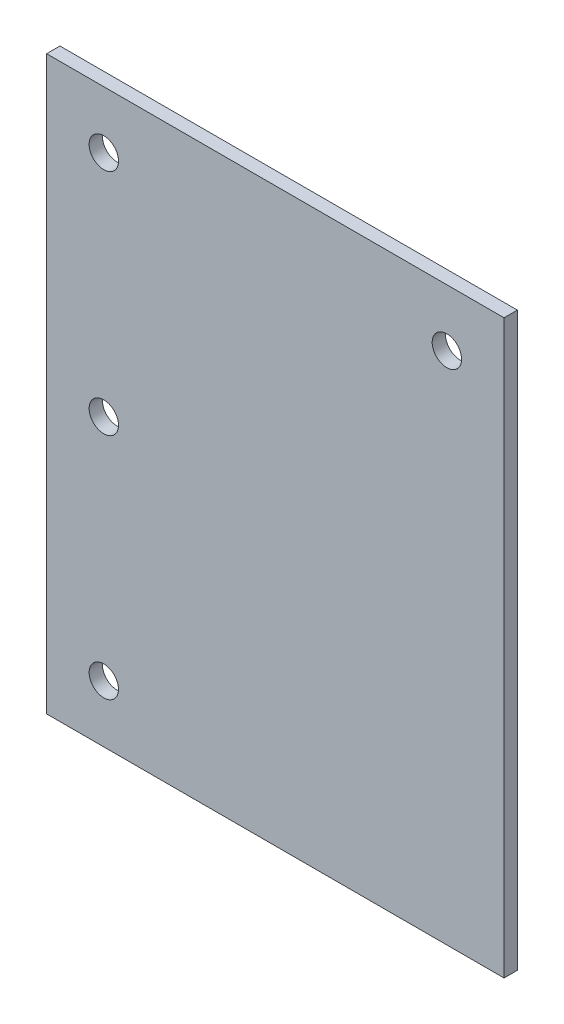
SolidWorks part; units mm, degrees
ref_plane "Front Plane" through (0, 0, 0) normal (0, 0, 1) x (1, 0, 0)
ref_plane "Top Plane" through (0, 0, 0) normal (0, 1, 0) x (1, 0, 0)
ref_plane "Right Plane" through (0, 0, 0) normal (1, 0, 0) x (0, 0, -1)
sketch "Sketch1" plane through (0, 0, 0) normal (0, 0, 1) x (1, 0, 0)
  line L1 (-50.8, 63.5) -> (50.8, 63.5)
  line L2 (-50.8, 63.5) -> (-50.8, -63.5)
  line L3 (-50.8, -63.5) -> (50.8, -63.5)
  line L4 (50.8, 63.5) -> (50.8, -63.5)
  line L5 (-50.8, 63.5) -> (50.8, -63.5) construction
  line L6 (-50.8, -63.5) -> (50.8, 63.5) construction
  point P0 (0, 0)
  dimension "D1" = 127
  dimension "D2" = 101.6
extrude "Boss-Extrude1" add sketch "Sketch1" along normal blind 2.9591 contours L1 L4 L3 L2
hole_wizard "1/4 Clearance Hole1" positions "Sketch3" profile "Sketch2" hole size "1/4" standard "ANSI Inch"
sketch "Sketch3" plane through (0, 0, 2.9591) normal (0, 0, 1) x (1, 0, 0)
  line L0 (-50.8, 63.5) -> (50.8, 63.5) construction
  line L1 (-50.8, 63.5) -> (-50.8, -63.5) construction
  point P0 (-38.1, 50.8)
  point P8 (38.1, 50.8)
  point P13 (-38.1, -50.8)
  point P18 (-38.1, 0)
  dimension "D4" = 101.6
  dimension "D1" = 12.7
  dimension "D2" = 12.7
  dimension "D3" = 76.2
sketch "Sketch2" plane through (-38.1, 50.8, 2.9591) normal (1, 0, 0) x (0, -1, 0)
  line L0 (0, 0) -> (0, 5.2631)
  line L1 (0, 5.2631) -> (3.2639, 3.302)
  line L2 (3.2639, 3.302) -> (3.2639, 0)
  line L5 (3.2639, 0) -> (0, 0)
  line L10 (0, 5.2631) -> (-3.2639, 3.302) construction
  line L11 (0, -6.35) -> (0, 107.95) construction
  dimension "Hole Dia." = 6.5278
  dimension "Hole Depth" = 3.302
  dimension "Drill Angle" = 118
